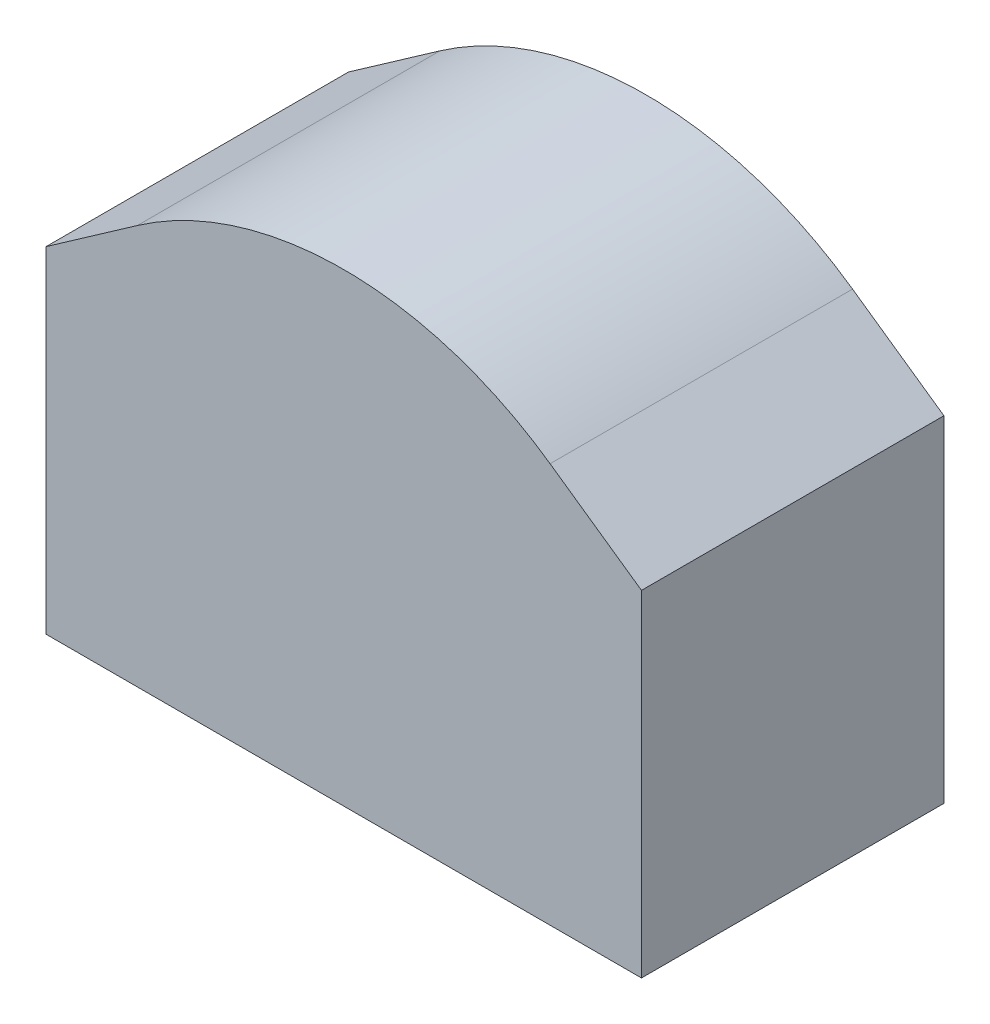
SolidWorks part; units mm, degrees
material "Acrylic (Medium-high impact)"
ref_plane "Front Plane" through (0, 0, 0) normal (0, 0, 1) x (1, 0, 0)
ref_plane "Top Plane" through (0, 0, 0) normal (0, 1, 0) x (1, 0, 0)
ref_plane "Right Plane" through (0, 0, 0) normal (1, 0, 0) x (0, 0, -1)
sketch "Sketch1" plane through (0, 0, 0) normal (0, 0, 1) x (1, 0, 0)
  line L0 (-2.65, -1.032) -> (2.65, -1.032)
  line L1 (2.65, -1.032) -> (2.65, 2.0151)
  line L2 (2.65, 2.0151) -> (1.8186, 2.5972)
  line L3 (-1.8186, 2.5972) -> (-2.65, 2.0151)
  line L4 (-2.65, 2.0151) -> (-2.65, -1.032)
  line L5 (-1.8186, 2.5972) -> (1.8186, 2.5972) construction
  line L6 (0.9, 3.0402) -> (-0.9, 3.0402) construction
  line L7 (-2.5, -0.882) -> (2.5, -0.882)
  line L8 (2.5, -0.882) -> (2.5, 1.937)
  line L9 (2.5, 1.937) -> (1.7326, 2.4744)
  line L10 (-1.7326, 2.4744) -> (-2.5, 1.937)
  line L11 (-2.5, 1.937) -> (-2.5, -0.882)
  arc A0 (1.8186, 2.5972) -> (0.9, 3.0402) centre (0, 0) ccw
  arc A1 (0.9, 3.0402) -> (-0.9, 3.0402) centre (0, 0) ccw
  arc A2 (-0.9, 3.0402) -> (-1.8186, 2.5972) centre (0, 0) ccw
  arc A3 (1.7326, 2.4744) -> (0.8574, 2.8964) centre (0, 0) ccw
  arc A4 (0.8574, 2.8964) -> (-0.8574, 2.8964) centre (0, 0) ccw
  arc A5 (-0.8574, 2.8964) -> (-1.7326, 2.4744) centre (0, 0) ccw
  point P11 (0, 3.0402)
  point P12 (0, 2.5972)
  point P19 (0, 3.1707)
  dimension "D1" = 5.3
  dimension "D2" = 3.0471
  dimension "D3" = 1.8
  dimension "D4" = 3.6372
  dimension "D5" = 0.443
  dimension "D6" = 0.15
extrude "Boss-Extrude1" add sketch "Sketch1" along normal blind 2.54 contours L7 L8 L9 A3 A4 A5 L10 L11
